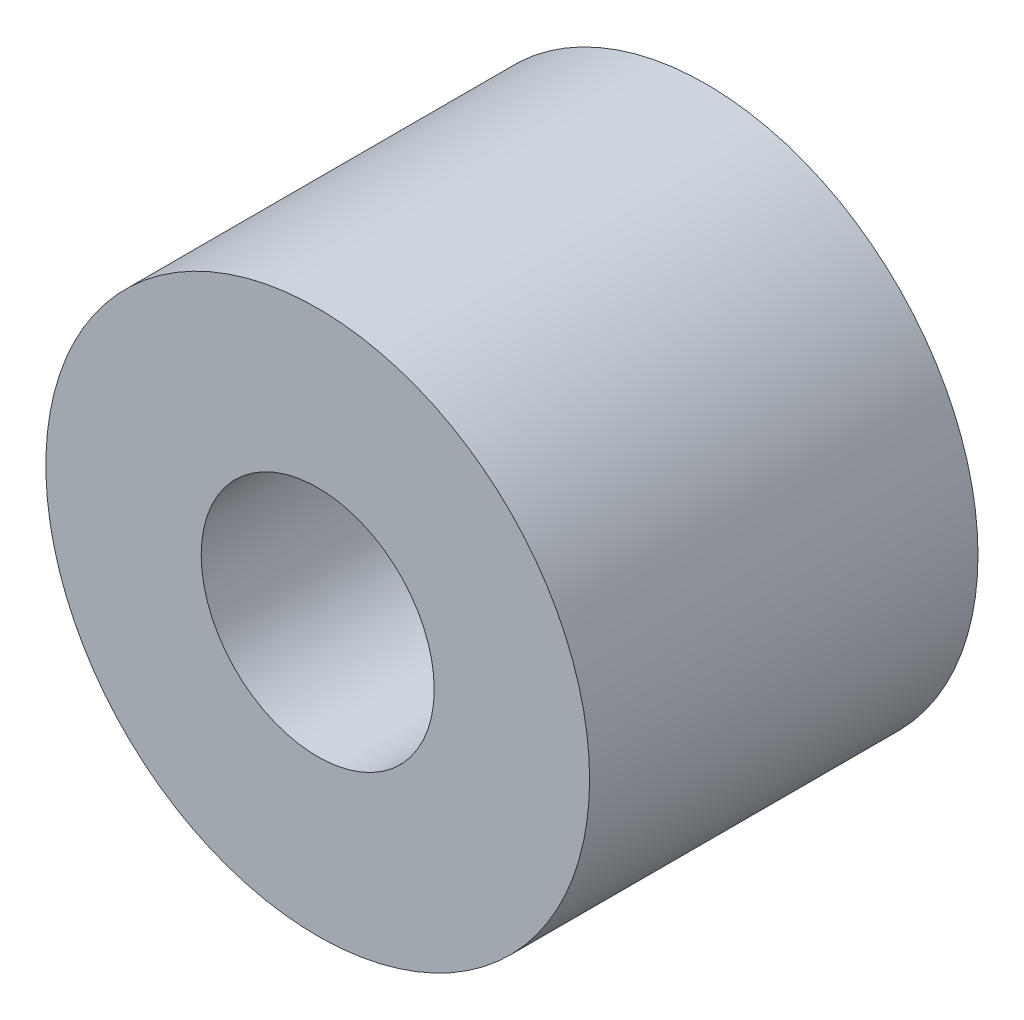
SolidWorks part; units mm, degrees
ref_plane "Plan de face" through (0, 0, 0) normal (0, 0, 1) x (1, 0, 0)
ref_plane "Plan de dessus" through (0, 0, 0) normal (0, 1, 0) x (1, 0, 0)
ref_plane "Plan de droite" through (0, 0, 0) normal (1, 0, 0) x (0, 0, -1)
sketch "Esquisse1" plane through (0, 0, 0) normal (0, 0, 1) x (1, 0, 0)
  circle A0 centre (-433.0689, 57.3068) radius 3.5
  circle A1 centre (-433.0689, 57.3068) radius 2.5 construction
  circle A3 centre (-433.0689, 57.3068) radius 2.5 construction
  arc A4 (-430.654, 57.9539) -> (-430.5689, 57.3068) centre (-433.0689, 57.3068) ccw construction
  circle A5 centre (-433.0689, 57.3068) radius 1.5
  dimension "D1" = 2
  dimension "D2" = 1
extrude "Boss.-Extru.1" add sketch "Esquisse1" along normal blind 5
